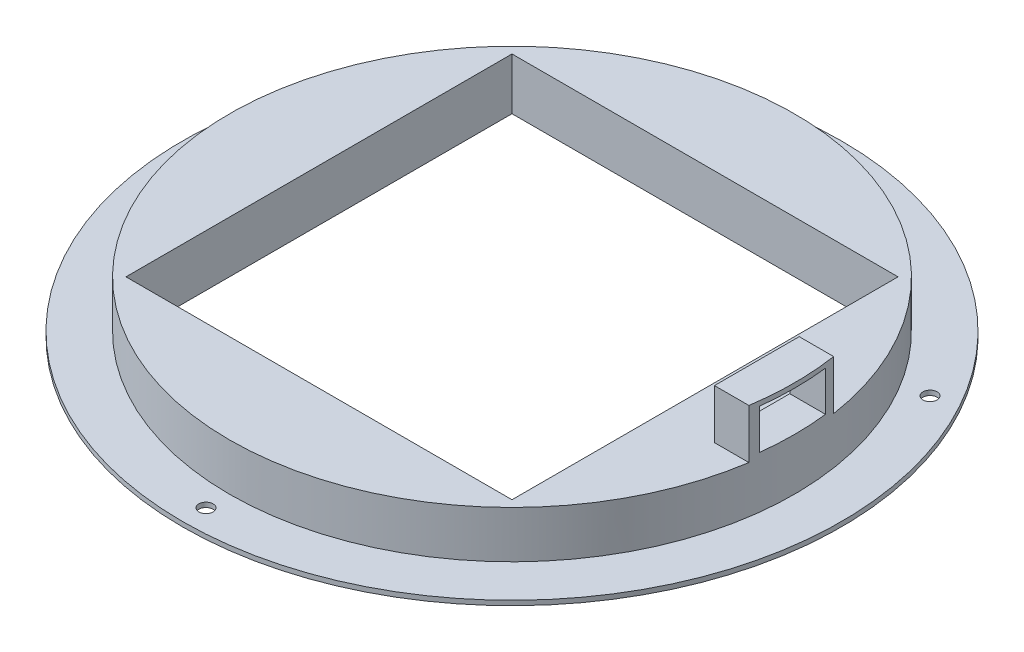
SolidWorks part; units mm, degrees
ref_plane "Alzado" through (0, 0, 0) normal (0, 0, 1) x (1, 0, 0)
ref_plane "Planta" through (0, 0, 0) normal (0, 1, 0) x (1, 0, 0)
ref_plane "Vista lateral" through (0, 0, 0) normal (1, 0, 0) x (0, 0, -1)
sketch "Croquis1" plane through (0, 0, 0) normal (0, 0, 1) x (1, 0, 0)
  line L0 (-96.9016, 61.9761) -> (-96.9016, 60.9761)
  line L1 (-69.9016, 46.9761) -> (-69.9016, -33.0239) construction
  line L2 (-67.9016, 46.9761) -> (14.0984, 46.9761) construction
  line L3 (-26.9016, 46.9761) -> (-26.9016, -33.0239) construction
  line L4 (-26.9016, -33.0239) -> (-101.9016, -33.0239) construction
  line L5 (-67.9016, 60.9761) -> (-67.9016, 61.9761)
  line L8 (-26.9016, 46.9761) -> (-26.9016, 61.9761) construction
  line L9 (-26.9016, 61.9761) -> (-86.9016, 61.9761) construction
  line L10 (-96.9016, 60.9761) -> (-67.9016, 60.9761)
  line L11 (-86.9016, 61.9761) -> (-96.9016, 61.9761)
  line L15 (-86.9016, 61.9761) -> (-86.9016, 71.9761)
  line L16 (-86.9016, 71.9761) -> (-67.9016, 71.9761)
  line L17 (-67.9016, 71.9761) -> (-67.9016, 61.9761)
  dimension "D1" = 19
  dimension "D2" = 10
revolve "Revolución1" add sketch "Croquis1" angle 360 about L3
sketch "Croquis2" plane through (0, 71.9761, 0) normal (0, 1, 0) x (1, 0, 0)
  line L1 (14.0984, -41) -> (-67.9016, -41)
  line L2 (14.0984, -41) -> (14.0984, 41)
  line L3 (14.0984, 41) -> (-67.9016, 41)
  line L4 (-67.9016, -41) -> (-67.9016, 41)
  line L5 (14.0984, -41) -> (-67.9016, 41) construction
  line L6 (14.0984, 41) -> (-67.9016, -41) construction
  point P0 (-26.9016, 0)
  dimension "D1" = 82
  dimension "D2" = 82
extrude "Cortar-Extruir1" cut sketch "Croquis2" against normal blind 11.5
sketch "Croquis3" plane through (0, 71.9761, 0) normal (0, 1, 0) x (1, 0, 0)
  line L0 (14.0984, -41) -> (14.0984, 41) construction
  line L3 (32.4195, 9) -> (25.0984, 9)
  line L4 (25.0984, 9) -> (25.0984, -9)
  line L5 (25.0984, -9) -> (32.4195, -9)
  arc A2 (32.4195, 9) -> (32.4195, -9) centre (-26.9016, 0) cw
extrude "Saliente-Extruir1" add sketch "Croquis3" along normal blind 10.5
sketch "Croquis4" plane through (25.0984, 0, 0) normal (-1, 0, 0) x (0, 0, 1)
  line L0 (-9, 71.9761) -> (9, 82.4761) construction
  line L1 (9, 82.4761) -> (9, 71.9761) construction
  line L2 (9, 71.9761) -> (-9, 82.4761) construction
  line L4 (-7, 81.4761) -> (7, 81.4761)
  line L5 (-7, 81.4761) -> (-7, 72.9761)
  line L6 (-7, 72.9761) -> (7, 72.9761)
  line L7 (7, 81.4761) -> (7, 72.9761)
  line L8 (-7, 81.4761) -> (7, 72.9761) construction
  line L9 (-7, 72.9761) -> (7, 81.4761) construction
  point P6 (0, 77.2261)
  dimension "D1" = 14
  dimension "D2" = 8.5
extrude "Cortar-Extruir2" cut sketch "Croquis4" against normal blind 10.5
sketch "Croquis5" plane through (0, 61.9761, 0) normal (0, 1, 0) x (1, 0, 0)
  line L0 (-26.9016, -70) -> (-26.9016, -60) construction
  line L1 (-26.9016, -70) -> (-26.9016, 70) construction
  line L2 (-26.9016, 0) -> (-35.8271, 0) construction
  circle A0 centre (-26.9016, 0) radius 70 construction
  circle A1 centre (-26.9016, 0) radius 60 construction
  circle A2 centre (-26.9016, -65) radius 1.5
  circle A3 centre (-83.1933, 32.5) radius 1.5
  circle A4 centre (29.39, 32.5) radius 1.5
  point P19 (-26.9016, 0)
  dimension "D1" = 3
extrude "Cortar-Extruir3" cut sketch "Croquis5" against normal blind 10
